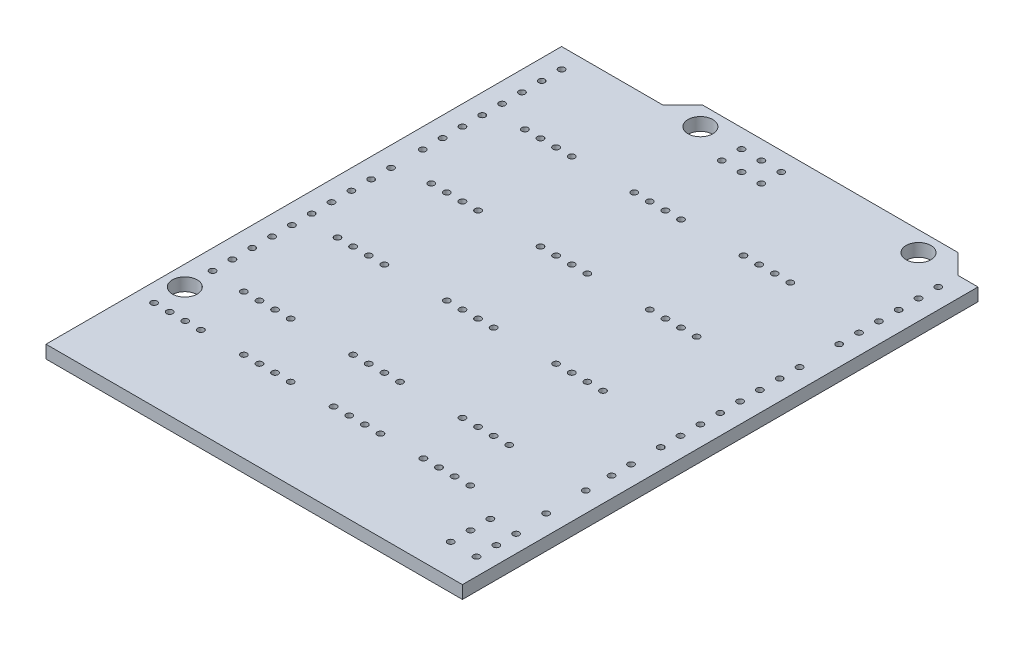
SolidWorks part; units mm, degrees
material "E-Glass Fiber"
ref_plane "Front Plane" through (0, 0, 0) normal (0, 0, 1) x (1, 0, 0)
ref_plane "Top Plane" through (0, 0, 0) normal (0, 1, 0) x (1, 0, 0)
ref_plane "Right Plane" through (0, 0, 0) normal (1, 0, 0) x (0, 0, -1)
sketch "Sketch1" plane through (0, 0, 0) normal (0, 1, 0) x (1, 0, 0)
  line L0 (-55, 0) -> (55, 0) construction
  line L1 (0, 0) -> (-53.34, 0)
  line L2 (0, 0) -> (0, 66.04)
  line L3 (-5.08, 68.58) -> (-37.846, 68.58)
  line L4 (-53.34, 0) -> (-53.34, 66.04)
  line L5 (-53.34, 66.04) -> (-40.386, 66.04)
  line L6 (-40.386, 66.04) -> (-37.846, 68.58)
  line L7 (-5.08, 68.58) -> (-2.54, 66.04)
  line L8 (-2.54, 66.04) -> (0, 66.04)
  circle A0 centre (-7.62, 66.04) radius 1.5875
  circle A1 centre (-35.56, 66.04) radius 1.5875
  circle A3 centre (-50.8, 15.24) radius 1.5875
  dimension "D8" = 3.175
  dimension "D1" = 68.58
  dimension "D2" = 53.34
  dimension "D3" = 66.04
  dimension "D4" = 2.54
  dimension "D5" = 45
  dimension "D6" = 45
  dimension "D7" = 40.386
  dimension "D9" = 66.04
  dimension "D10" = 35.56
  dimension "D11" = 7.62
  dimension "D14" = 15.24
  dimension "D15" = 50.8
extrude "Boss-Extrude1" add sketch "Sketch1" against normal blind 1.65
sketch "Sketch2" plane through (0, 0, 0) normal (0, 1, 0) x (1, 0, 0)
  line L0 (0, -0.9075) -> (0, 0.9075) construction
  line L1 (-0.9075, 0) -> (0.9075, 0) construction
  circle A0 centre (-2.54, 27.94) radius 0.4
  dimension "D1" = 0.8
  dimension "D2" = 2.54
  dimension "D3" = 27.94
extrude "Cut-Extrude1" cut sketch "Sketch2" against normal blind 1.65
sketch "Sketch3" plane through (0, 0, 0) normal (0, 1, 0) x (1, 0, 0)
  line L0 (0, -0.9075) -> (0, 0.9075) construction
  line L1 (-0.9075, 0) -> (0.9075, 0) construction
  circle A0 centre (-50.8, 18.796) radius 0.4
  dimension "D2" = 0.8
  dimension "D1" = 50.8
  dimension "D3" = 18.796
extrude "Cut-Extrude2" cut sketch "Sketch3" against normal blind 1.65
pattern_linear "LPattern1" count 15 spacing 2.54 along (0, 0, -1) skipping (8, 0) of "Cut-Extrude1"
sketch "Sketch4" plane through (0, 0, 0) normal (0, 1, 0) x (1, 0, 0)
  line L0 (-0.9075, 0) -> (0.9075, 0) construction
  line L1 (0, -0.9075) -> (0, 0.9075) construction
  circle A0 centre (-50.8, 45.72) radius 0.4
  dimension "D3" = 0.8
  dimension "D1" = 45.72
  dimension "D2" = 50.8
extrude "Cut-Extrude3" cut sketch "Sketch4" against normal blind 1.65
pattern_linear "LPattern2" count 10 spacing 2.54 along (0, 0, -1) of "Cut-Extrude2"
pattern_linear "LPattern3" count 8 spacing 2.54 along (0, 0, -1) of "Cut-Extrude3"
sketch "Sketch5" plane through (0, 0, 0) normal (0, 1, 0) x (1, 0, 0)
  line L0 (-27.89, 66.18) -> (-27.89, 63.64) construction
  line L1 (-30.43, 66.18) -> (-25.35, 66.18) construction
  line L2 (-30.43, 66.18) -> (-30.43, 63.64) construction
  line L3 (-30.43, 63.64) -> (-25.35, 63.64) construction
  line L4 (-25.35, 66.18) -> (-25.35, 63.64) construction
  line L5 (-0.9075, 0) -> (0.9075, 0) construction
  line L6 (0, -0.9075) -> (0, 0.9075) construction
  line L7 (0, 0) -> (0, 66.04) construction
  circle A0 centre (-30.43, 66.18) radius 0.4
  circle A1 centre (-27.89, 66.18) radius 0.4
  circle A2 centre (-25.35, 66.18) radius 0.4
  circle A3 centre (-25.35, 63.64) radius 0.4
  circle A4 centre (-27.89, 63.64) radius 0.4
  circle A5 centre (-30.43, 63.64) radius 0.4
  circle A6 centre (-5.5, 4) radius 0.4
  circle A7 centre (-5.5, 6.54) radius 0.4
  circle A8 centre (-5.5, 9.08) radius 0.4
  circle A9 centre (-2.2, 9.08) radius 0.4
  circle A10 centre (-2.2, 6.54) radius 0.4
  circle A11 centre (-2.2, 4) radius 0.4
  circle A12 centre (-2.54, 24.14) radius 0.4
  circle A13 centre (-2.54, 21.64) radius 0.4
  circle A14 centre (-2.54, 18.34) radius 0.4
  circle A15 centre (-2.54, 13.26) radius 0.4
  circle A16 centre (-2.54, 27.94) radius 0.4 construction
  dimension "D4" = 0.8
  dimension "D14" = 9.6
  dimension "D10" = 3.8
  dimension "D11" = 2.5
  dimension "D15" = 5.08
  dimension "D1" = 2.54
  dimension "D2" = 2.54
  dimension "D3" = 2.54
  dimension "D5" = 63.64
  dimension "D6" = 30.43
  dimension "D7" = 2.54
  dimension "D8" = 2.54
  dimension "D9" = 3.3
  dimension "D12" = 5.5
  dimension "D13" = 4
  dimension "D16" = 2.54
extrude "Cut-Extrude4" cut sketch "Sketch5" against normal blind 10
sketch "Esquisse1" plane through (0, -1.65, 0) normal (0, -1, 0) x (1, 0, 0)
  line L0 (-53.34, 0) -> (0, 0) construction
  line L1 (0, 0) -> (0, -66.04) construction
  circle A0 centre (-10.5, -11.5) radius 0.4
  circle A1 centre (-5.5, -6.54) radius 0.4 construction
  dimension "D1" = 11.5
  dimension "D2" = 10.5
extrude "Enlèv. mat.-Extru.1" cut sketch "Esquisse1" against normal blind 10
pattern_linear "Répétition linéaire1" count 4 spacing 2 along (-1, 0, 0) count 4 spacing 11.5 along (-1, 0, 0) of "Enlèv. mat.-Extru.1"
sketch "Esquisse2" plane through (0, -1.65, 0) normal (0, -1, 0) x (1, 0, 0)
  line L0 (0, 0) -> (0, -66.04) construction
  line L1 (-53.34, 0) -> (0, 0) construction
  circle A0 centre (-12.5, -18.5) radius 0.4
  circle A1 centre (-10.5, -11.5) radius 0.4 construction
  dimension "D1" = 12.5
  dimension "D2" = 18.5
extrude "Enlèv. mat.-Extru.2" cut sketch "Esquisse2" against normal blind 10
pattern_linear "Répétition linéaire2" count 4 spacing 2 along (-1, 0, 0) count 3 spacing 14 along (-1, 0, 0) of "Enlèv. mat.-Extru.2"
pattern_linear "Répétition linéaire3" count 4 spacing 12 along (0, 0, -1) of "Répétition linéaire2", "Enlèv. mat.-Extru.2"
equation "\"D16@Sketch5\" = 645 * 0.001 * 25.4"
